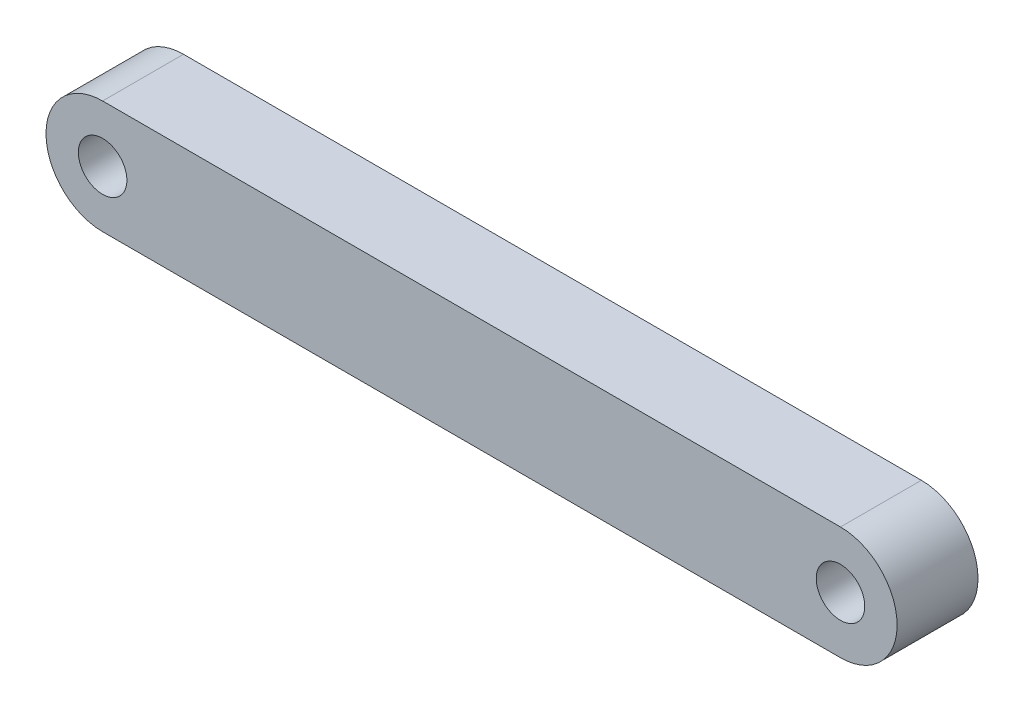
SolidWorks part; units mm, degrees
ref_plane "Front Plane" through (0, 0, 0) normal (0, 0, 1) x (1, 0, 0)
ref_plane "Top Plane" through (0, 0, 0) normal (0, 1, 0) x (1, 0, 0)
ref_plane "Right Plane" through (0, 0, 0) normal (1, 0, 0) x (0, 0, -1)
sketch "Sketch1" plane through (0, 0, 0) normal (0, 0, 1) x (1, 0, 0)
  line L0 (0, 3.5) -> (-45.61, 3.5)
  line L1 (0, -3.5) -> (-45.61, -3.5)
  circle A0 centre (0, 0) radius 1.5
  circle A1 centre (0, 0) radius 3.5
  arc A2 (-45.61, 3.5) -> (-45.61, -3.5) centre (-45.61, 0) ccw
  circle A3 centre (-45.61, 0) radius 1.5
  dimension "D2" = 3
  dimension "D4" = 3
  dimension "D3" = 45.61
  dimension "D1" = 2
extrude "Boss-Extrude1" add sketch "Sketch1" along normal blind 5 contours L0 A2 L1 A1 | A1 A0
equation "\"D4@Sketch1\"=\"D2@Sketch1\""
